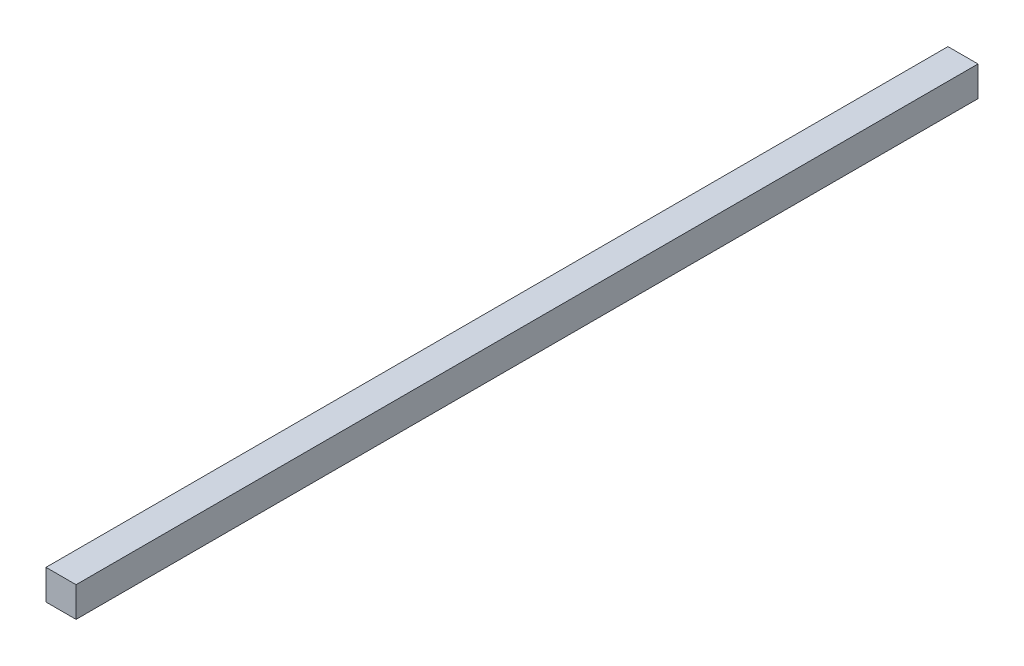
SolidWorks part; units mm, degrees
material "Plain Carbon Steel"
ref_plane "Front Plane" through (0, 0, 0) normal (0, 0, 1) x (1, 0, 0)
ref_plane "Top Plane" through (0, 0, 0) normal (0, 1, 0) x (1, 0, 0)
ref_plane "Right Plane" through (0, 0, 0) normal (1, 0, 0) x (0, 0, -1)
sketch "Sketch1" plane through (0, 0, 0) normal (0, 0, 1) x (1, 0, 0)
  line L1 (0, 0) -> (10, 0)
  line L2 (0, 0) -> (0, 10)
  line L3 (0, 10) -> (10, 10)
  line L4 (10, 0) -> (10, 10)
  dimension "D1" = 10
  dimension "D2" = 10
extrude "Boss-Extrude1" add sketch "Sketch1" along normal blind 300
